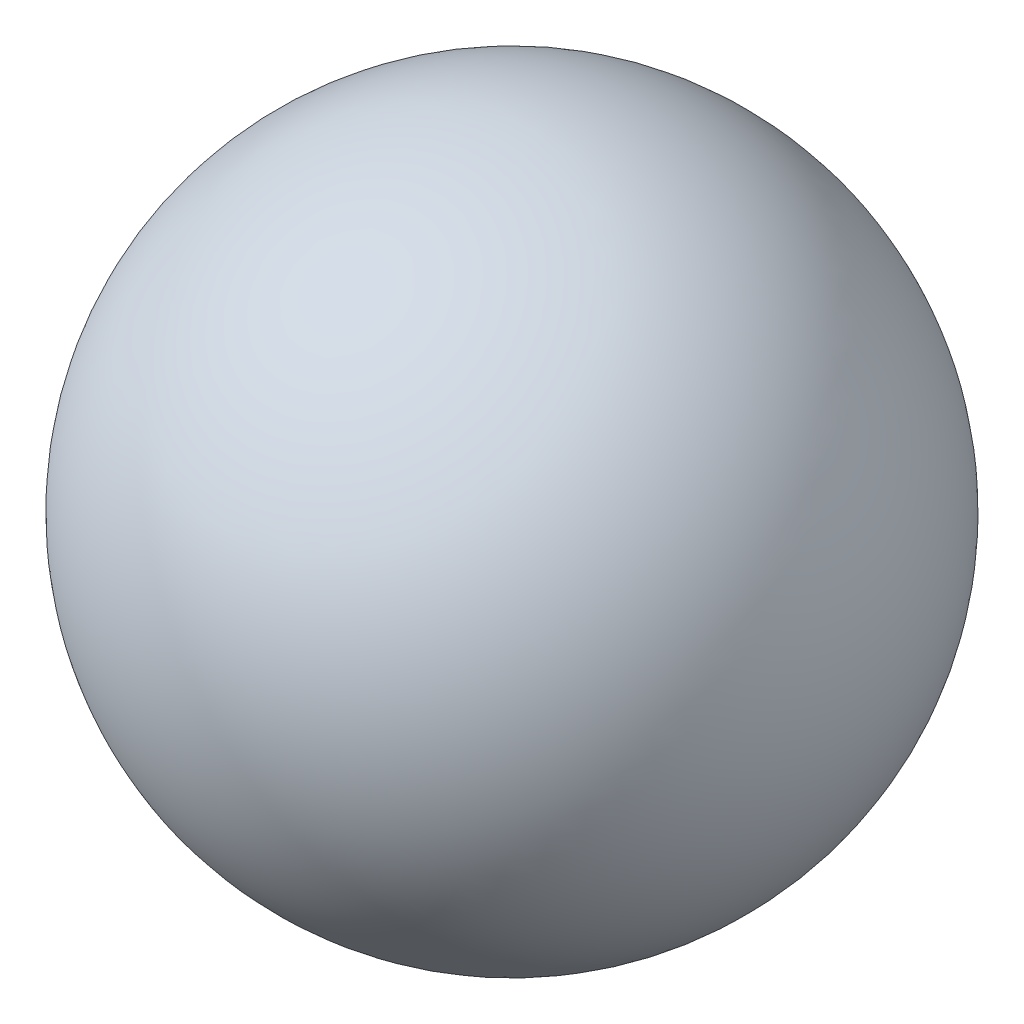
SolidWorks part; units mm, degrees
ref_plane "Front Plane" through (0, 0, 0) normal (0, 0, 1) x (1, 0, 0)
ref_plane "Top Plane" through (0, 0, 0) normal (0, 1, 0) x (1, 0, 0)
ref_plane "Right Plane" through (0, 0, 0) normal (1, 0, 0) x (0, 0, -1)
sketch "Sketch1" plane through (0, 0, 0) normal (0, 1, 0) x (1, 0, 0)
  line L0 (0, 0) -> (0, -50000) construction
  line L1 (0, 2.9) -> (0, -2.9)
  arc A0 (0, 2.9) -> (0, -2.9) centre (0, 0) ccw
  dimension "D1" = 5.8
revolve "Revolve1" add sketch "Sketch1" angle 360 about L0
sketch "Sketch2" plane through (0, 0, 0) normal (0, 0, 1) x (1, 0, 0)
  point P0 (0, 0)
  point P1 (-2.9, 0)
  point P2 (0, 0)
  point P4 (-2.9, 0)
  point P5 (0, 0)
  point P6 (0, 0)
  point P7 (-2.8849, 0.2957)
